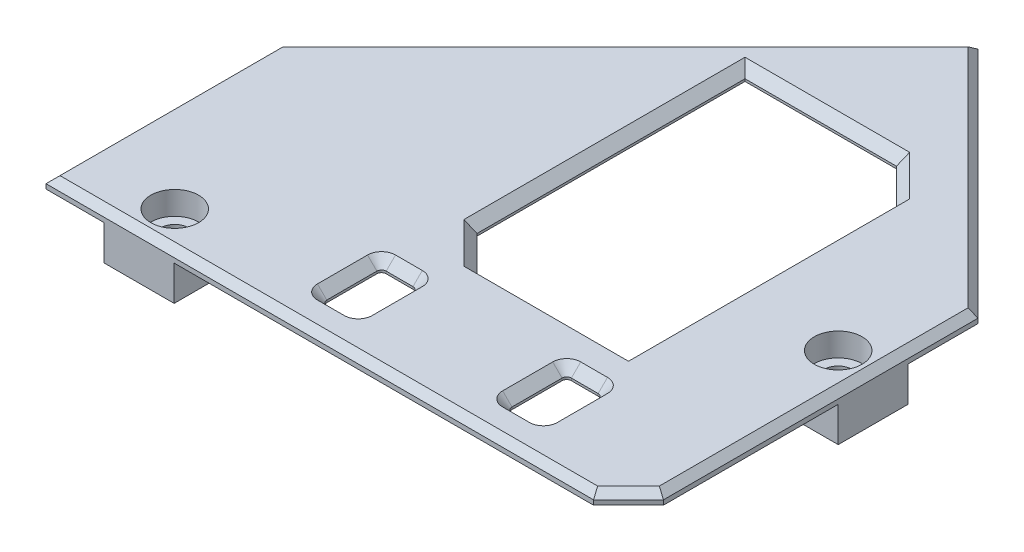
SolidWorks part; units mm, degrees
ref_plane "前视基准面" through (0, 0, 0) normal (0, 0, 1) x (1, 0, 0)
ref_plane "上视基准面" through (0, 0, 0) normal (0, 1, 0) x (1, 0, 0)
ref_plane "右视基准面" through (0, 0, 0) normal (1, 0, 0) x (0, 0, -1)
sketch "草图1" plane through (0, 0, 0) normal (0, 1, 0) x (1, 0, 0)
  line L0 (0, 0) -> (50, 0)
  line L1 (50, 0) -> (50, 30)
  line L2 (50, 30) -> (30, 50)
  line L3 (30, 50) -> (0, 20)
  line L4 (0, 20) -> (0, 0)
  dimension "D1" = 135
  dimension "D2" = 50
  dimension "D3" = 20
  dimension "D4" = 20
extrude "凸台-拉伸1" add sketch "草图1" along normal blind 1
chamfer "倒角2" distance 3 angle 45 1 edges at (50, 0.5, 0)
chamfer "倒角1" distance 0.6 angle 45 6 edges at (50, 1, -16.5) (23.5, 1, 0) (0, 1, -10) (48.5, 1, -1.5) (40, 1, -40) (15, 1, -35)
sketch "草图2" plane through (0, 1, 0) normal (0, 1, 0) x (1, 0, 0)
  line L0 (50, 30) -> (50, 3) construction
  line L1 (22, 38) -> (38, 38)
  line L2 (22, 38) -> (22, 12)
  line L3 (22, 12) -> (38, 12)
  line L4 (38, 38) -> (38, 12)
  line L5 (47, 0) -> (0, 0) construction
  dimension "D1" = 26
  dimension "D2" = 16
  dimension "D3" = 12
  dimension "D4" = 12
extrude "切除-拉伸1" cut sketch "草图2" against normal blind 10
chamfer "倒角3" distance 3 angle 45 2 edges at (38, 0.5, -38) (22, 0.5, -12)
chamfer "倒角4" distance 0.8 angle 45 6 edges at (28.5, 1, -38) (36.5, 1, -36.5) (38, 1, -23.5) (22, 1, -26.5) (31.5, 1, -12) (23.5, 1, -13.5)
sketch "草图3" plane through (0, 0, 0) normal (0, -1, 0) x (1, 0, 0)
  line L0 (0, 0) -> (47, 0) construction
  line L1 (5, 0) -> (11, 0)
  line L2 (5, 0) -> (5, -6)
  line L3 (5, -6) -> (11, -6)
  line L4 (11, 0) -> (11, -6)
  line L5 (50, -3) -> (50, -30) construction
  line L6 (50, -18) -> (44, -18)
  line L7 (50, -18) -> (50, -24)
  line L8 (50, -24) -> (44, -24)
  line L9 (44, -18) -> (44, -24)
  dimension "D1" = 6
  dimension "D2" = 5
  dimension "D3" = 6
  dimension "D4" = 18
  dimension "D5" = 6
  dimension "D6" = 6
extrude "凸台-拉伸2" add sketch "草图3" along normal blind 3
sketch "草图4" plane through (0, -3, 0) normal (0, -1, 0) x (1, 0, 0)
  circle A0 centre (8, -3.05) radius 1.2
  circle A1 centre (47, -21) radius 1.2
  dimension "D1" = 2.4
  dimension "D2" = 2.4
extrude "切除-拉伸2" cut sketch "草图4" against normal through all
sketch "草图5" plane through (0, 1, 0) normal (0, 1, 0) x (1, 0, 0)
  circle A0 centre (8, 3.05) radius 2.05
  circle A1 centre (47, 21) radius 2.05
  dimension "D1" = 4.1
  dimension "D2" = 4.1
extrude "切除-拉伸3" cut sketch "草图5" against normal blind 2
fillet "圆角1" radius 2 4 edges at (5, -1.5, -6) (11, -1.5, -6) (44, -1.5, -18) (44, -1.5, -24)
sketch "草图7" plane through (0, 1, 0) normal (0, 1, 0) x (1, 0, 0)
  line L8 (36.3975, 8.3) -> (39.4975, 8.3)
  line L9 (39.4975, 8.3) -> (39.4975, 3.2)
  line L10 (36.3975, 3.2) -> (36.3975, 8.3)
  line L11 (39.4975, 3.2) -> (36.3975, 3.2)
  line L12 (23.6004, 8.3) -> (23.6004, 3.2)
  line L13 (23.6004, 3.2) -> (20.5004, 3.2)
  line L14 (20.5004, 3.2) -> (20.5004, 8.3)
  line L15 (20.5004, 8.3) -> (23.6004, 8.3)
extrude "切除-拉伸4" cut sketch "草图7" against normal blind 2 contours L15 L14 L13 L12 | L11 L9 L8 L10
fillet "圆角2" radius 0.4 8 edges at (36.3975, 0.5, -3.2) (36.3975, 0.5, -8.3) (39.4975, 0.5, -8.3) (39.4975, 0.5, -3.2) (23.6004, 0.5, -3.2) (23.6004, 0.5, -8.3) (20.5004, 0.5, -8.3) (20.5004, 0.5, -3.2)
chamfer "倒角5" distance 0.8 angle 45 16 edges at (36.3975, 1, -5.75) (37.9475, 1, -3.2) (39.4975, 1, -5.75) (37.9475, 1, -8.3) (22.0504, 1, -8.3) (23.6004, 1, -5.75) (22.0504, 1, -3.2) (20.5004, 1, -5.75) (36.5146, 1, -3.3172) (39.3803, 1, -3.3172) (36.5146, 1, -8.1828) (39.3803, 1, -8.1828) (23.4832, 1, -3.3172) (23.4832, 1, -8.1828) (20.6175, 1, -3.3172) (20.6175, 1, -8.1828)
